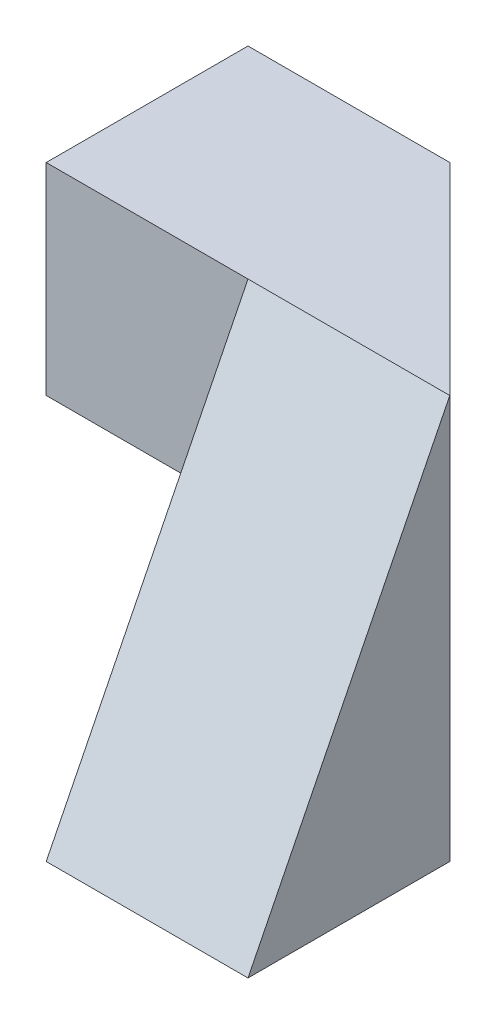
SolidWorks part; units mm, degrees
ref_plane "Front Plane" through (0, 0, 0) normal (0, 0, 1) x (1, 0, 0)
ref_plane "Top Plane" through (0, 0, 0) normal (0, 1, 0) x (1, 0, 0)
ref_plane "Right Plane" through (0, 0, 0) normal (1, 0, 0) x (0, 0, -1)
sketch "Sketch1" plane through (0, 0, 0) normal (0, 0, 1) x (1, 0, 0)
  line L1 (0, 0) -> (40, 0)
  line L2 (0, 0) -> (0, 40)
  line L3 (0, 40) -> (40, 40)
  line L4 (40, 0) -> (40, 40)
  dimension "D1" = 40
  dimension "D2" = 40
extrude "Boss-Extrude1" add sketch "Sketch1" along normal blind 40
sketch "Sketch2" plane through (0, 0, 40) normal (0, 0, 1) x (1, 0, 0)
  line L1 (0, 0) -> (20, 0)
  line L2 (0, 0) -> (0, 20)
  line L3 (0, 20) -> (20, 20)
  line L4 (20, 0) -> (20, 20)
  dimension "D1" = 20
  dimension "D2" = 20
extrude "Cut-Extrude1" cut sketch "Sketch2" against normal blind 40
sketch "Sketch3" plane through (0, 0, 0) normal (-1, 0, 0) x (0, 0, 1)
  line L0 (20, 40) -> (40, 0)
  line L1 (40, 40) -> (0, 40) construction
  line L2 (40, 0) -> (40, 40)
  line L3 (40, 40) -> (20, 40)
  dimension "D1" = 40
extrude "Cut-Extrude2" cut sketch "Sketch3" against normal blind 40
sketch "Sketch4" plane through (0, 0, 0) normal (0, -1, 0) x (-1, 0, 0)
  line L1 (-20, -40) -> (0, -40)
  line L2 (-20, -40) -> (-20, -20)
  line L3 (-20, -20) -> (0, -20)
  line L4 (0, -40) -> (0, -20)
  dimension "D1" = 20
  dimension "D2" = 20
extrude "Cut-Extrude3" cut sketch "Sketch4" against normal blind 40
sketch "Sketch5" plane through (0, 40, 0) normal (0, 1, 0) x (1, 0, 0)
  line L0 (20, 0) -> (40, -20)
  line L1 (40, 0) -> (0, 0) construction
  line L2 (40, -20) -> (40, 0)
  line L3 (40, 0) -> (20, 0)
extrude "Cut-Extrude4" cut sketch "Sketch5" against normal blind 40
